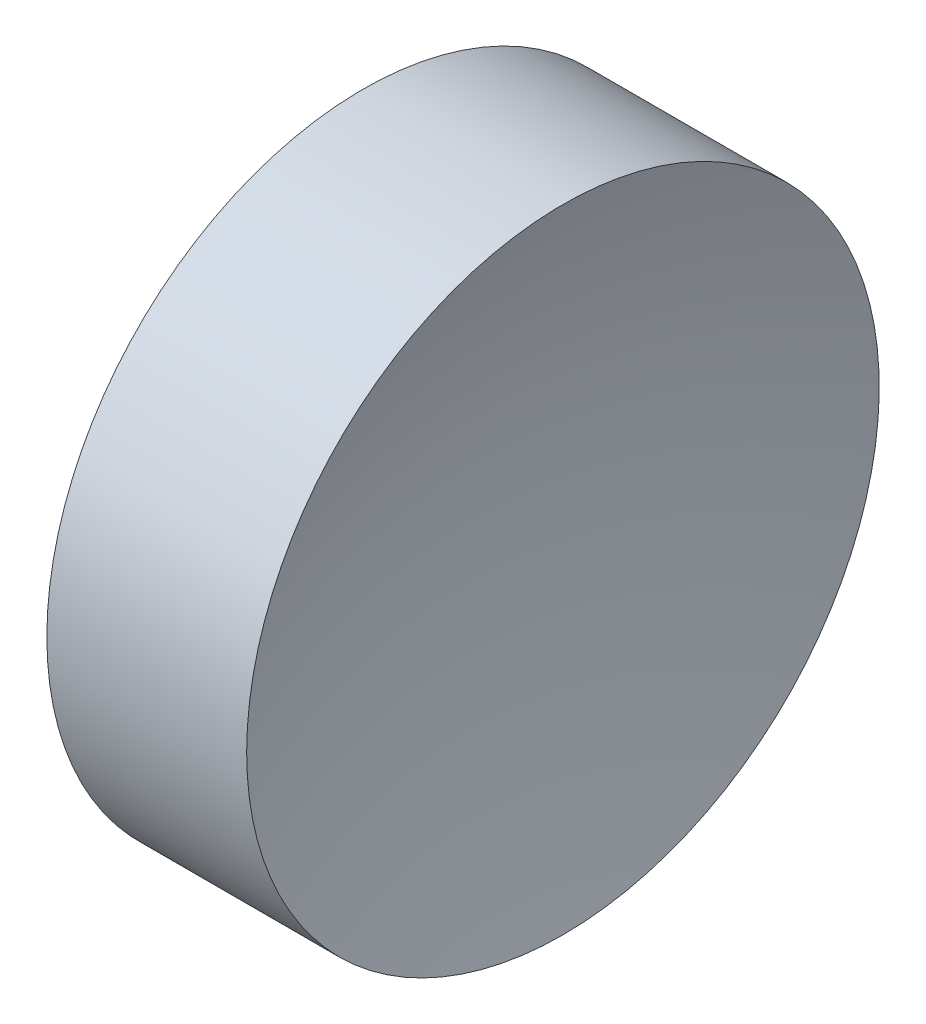
SolidWorks part; units mm, degrees
ref_plane "前视基准面" through (0, 0, 0) normal (0, 0, 1) x (1, 0, 0)
ref_plane "上视基准面" through (0, 0, 0) normal (0, 1, 0) x (1, 0, 0)
ref_plane "右视基准面" through (0, 0, 0) normal (1, 0, 0) x (0, 0, -1)
sketch "草图1" plane through (0, 0, 0) normal (0, 0, 1) x (1, 0, 0)
  line L0 (21.2249, 13.0445) -> (26.692, 13.0445) construction
  line L1 (22.1722, 13.0445) -> (22.1722, 16.1945)
  line L2 (23.6722, 13.0445) -> (22.1722, 13.0445)
  line L3 (22.1722, 16.1945) -> (24.1622, 16.1945)
  arc A0 (24.1622, 16.1945) -> (23.6722, 13.0445) centre (34.0422, 13.0445) ccw
revolve "旋转1" add sketch "草图1" angle 360 about L0
